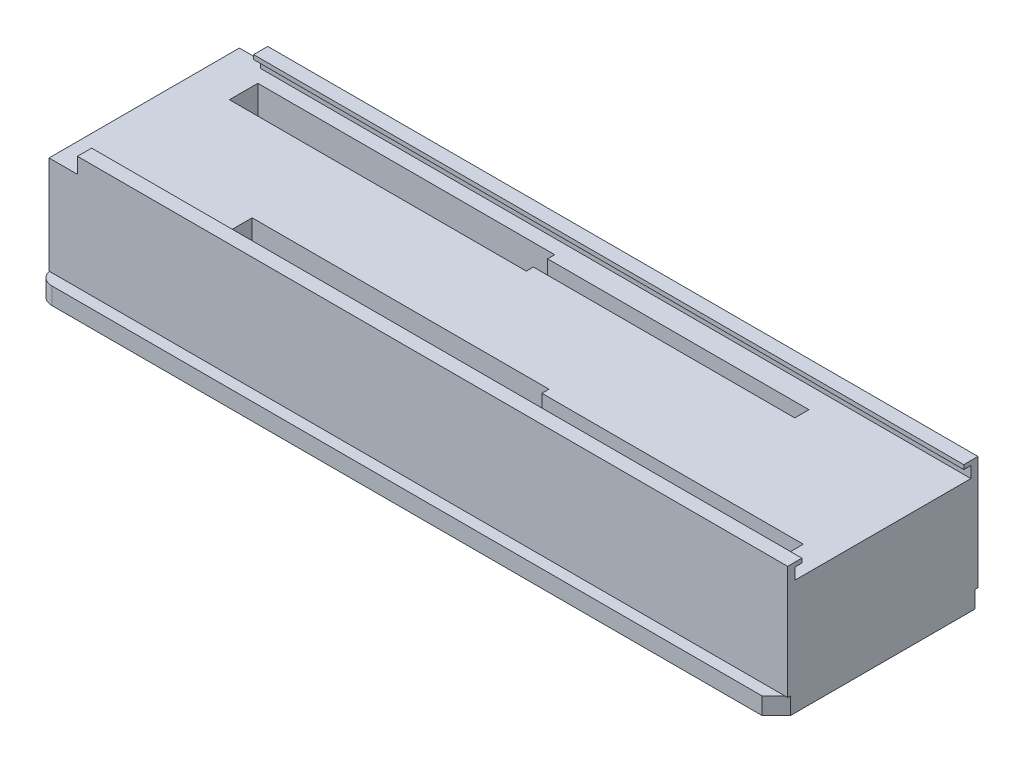
SolidWorks part; units mm, degrees
ref_plane "Front Plane" through (0, 0, 0) normal (0, 0, 1) x (1, 0, 0)
ref_plane "Top Plane" through (0, 0, 0) normal (0, 1, 0) x (1, 0, 0)
ref_plane "Right Plane" through (0, 0, 0) normal (1, 0, 0) x (0, 0, -1)
sketch "Sketch1" plane through (0, 0, 0) normal (0, 1, 0) x (1, 0, 0)
  line L1 (0, 0) -> (260, 0)
  line L2 (0, 0) -> (0, 75)
  line L3 (0, 75) -> (260, 75)
  line L4 (260, 0) -> (260, 75)
  dimension "D1" = 260
  dimension "D2" = 75
extrude "Boss-Extrude1" add sketch "Sketch1" along normal blind 6
chamfer "Chamfer1" distance 5 angle 45 2 edges at (260, 3, 0) (260, 3, -75)
fillet "Fillet1" radius 5 2 edges at (0, 3, -75) (0, 3, 0)
sketch "Sketch2" plane through (0, 6, 0) normal (0, 1, 0) x (1, 0, 0)
  line L0 (0, 70) -> (0, 5) construction
  line L1 (0, 71) -> (260, 71)
  line L2 (0, 71) -> (0, 4)
  line L3 (0, 4) -> (260, 4)
  line L4 (260, 71) -> (260, 4)
  line L5 (260, 5) -> (260, 70) construction
  line L6 (255, 75) -> (5, 75) construction
  line L7 (5, 0) -> (255, 0) construction
  dimension "D1" = 4
  dimension "D2" = 4
extrude "Boss-Extrude2" add sketch "Sketch2" along normal blind 40
sketch "Sketch3" plane through (0, 0, 0) normal (-1, 0, 0) x (0, 0, 1)
  line L0 (-66, 46) -> (-66, 44.5)
  line L1 (-71, 46) -> (-4, 46) construction
  line L2 (-66, 44.5) -> (-68.5, 44.5)
  line L3 (-68.5, 44.5) -> (-68.5, 40.5)
  line L4 (-68.5, 40.5) -> (-6.5, 40.5)
  line L5 (-6.5, 40.5) -> (-6.5, 44.5)
  line L6 (-6.5, 44.5) -> (-9, 44.5)
  line L7 (-9, 44.5) -> (-9, 46)
  line L8 (-9, 46) -> (-66, 46)
  line L9 (-71, 46) -> (-71, 6) construction
  line L10 (-4, 46) -> (-4, 6) construction
  point P4 (-37.5, 46)
  point P11 (-37.5, 40.5)
  dimension "D1" = 1.5
  dimension "D2" = 2.5
  dimension "D3" = 2.5
  dimension "D4" = 4
  dimension "D5" = 2.5
extrude "Cut-Extrude1" cut sketch "Sketch3" against normal through all
sketch "Sketch4" plane through (0, 46, 0) normal (0, 1, 0) x (1, 0, 0)
  line L0 (0, 4) -> (260, 4) construction
  line L1 (0, 71) -> (10, 71)
  line L2 (0, 71) -> (0, 4)
  line L3 (0, 4) -> (10, 4)
  line L4 (10, 71) -> (10, 4)
  line L7 (0, 71) -> (0, 66) construction
  point P9 (0, 0)
  dimension "D1" = 10
extrude "Cut-Extrude3" cut sketch "Sketch4" against normal up to surface (5.5 mm away) contours L4 L3 L2 L1 up to face at (130, 40.5, -37.5)
sketch "Sketch5" plane through (0, 40.5, 0) normal (0, 1, 0) x (1, 0, 0)
  line L8 (14, 63.5) -> (14, 53.5)
  line L9 (14, 53.5) -> (118.5, 53.5)
  line L10 (118.5, 53.5) -> (118.5, 56)
  line L11 (118.5, 56) -> (210.5, 56)
  line L12 (210.5, 56) -> (210.5, 61)
  line L13 (210.5, 61) -> (118.5, 61)
  line L14 (118.5, 61) -> (118.5, 63.5)
  line L15 (118.5, 63.5) -> (14, 63.5)
  line L17 (0, 71) -> (0, 4) construction
  line L18 (260, 68.5) -> (260, 6.5) construction
  line L20 (54, 21.5) -> (54, 11.5)
  line L21 (54, 11.5) -> (158.5, 11.5)
  line L22 (158.5, 11.5) -> (158.5, 14)
  line L23 (158.5, 14) -> (250.5, 14)
  line L24 (250.5, 14) -> (250.5, 19)
  line L25 (250.5, 19) -> (158.5, 19)
  line L26 (158.5, 19) -> (158.5, 21.5)
  line L27 (158.5, 21.5) -> (54, 21.5)
  point P0 (54, 16.5)
  point P2 (250.5, 16.5)
  point P10 (14, 58.5)
  point P12 (210.5, 58.5)
  point P30 (0, 0)
  dimension "D7" = 10
  dimension "D2" = 10
  dimension "D3" = 5
  dimension "D4" = 9.5
  dimension "D5" = 10
  dimension "D6" = 14
  dimension "D9" = 49.5
  dimension "D10" = 92
  dimension "D11" = 92
  dimension "D12" = 104.5
  dimension "D14" = 10
  dimension "D15" = 5
extrude "Cut-Extrude4" cut sketch "Sketch5" against normal blind 35
sketch "Sketch6" plane through (0, 5.5, 0) normal (0, 1, 0) x (1, 0, 0)
  line L0 (260, 68.5) -> (260, 6.5) construction
  line L1 (210.5, 61) -> (118.5, 61) construction
  line L2 (250.5, 19) -> (158.5, 19) construction
  circle A0 centre (208, 58.5) radius 2.5
  circle A1 centre (248, 16.5) radius 2.5
  dimension "D1" = 5
  dimension "D4" = 5
  dimension "D2" = 52
  dimension "D3" = 2.5
  dimension "D5" = 12
  dimension "D6" = 2.5
extrude "Cut-Extrude5" cut sketch "Sketch6" against normal through all
sketch "Sketch7" plane through (0, 0, 0) normal (0, -1, 0) x (1, 0, 0)
  line L0 (260, -5) -> (260, -70) construction
  circle A0 centre (170, -37.5) radius 3
  point P6 (260, -37.5)
  dimension "D1" = 6
  dimension "D2" = 90
extrude "Cut-Extrude6" cut sketch "Sketch7" against normal blind 5
